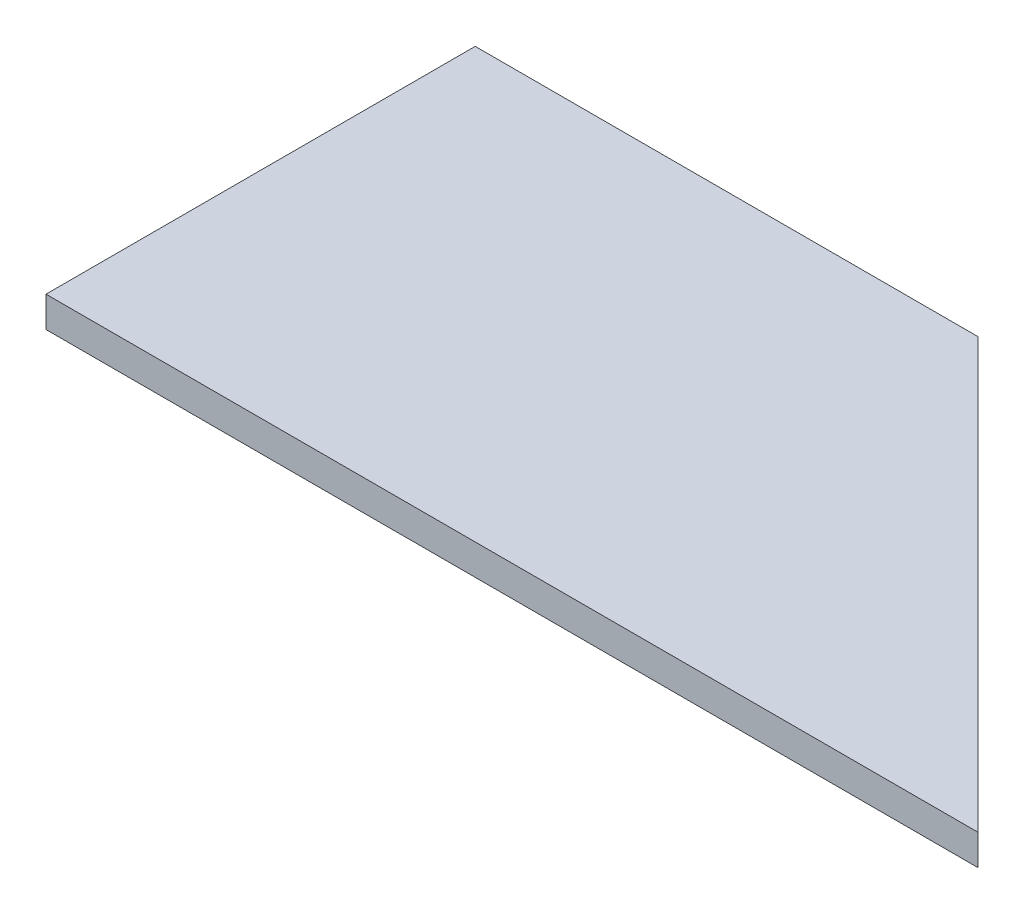
SolidWorks part; units mm, degrees
ref_plane "Front Plane" through (0, 0, 0) normal (0, 0, 1) x (1, 0, 0)
ref_plane "Top Plane" through (0, 0, 0) normal (0, 1, 0) x (1, 0, 0)
ref_plane "Right Plane" through (0, 0, 0) normal (1, 0, 0) x (0, 0, -1)
sketch "Sketch1" plane through (0, 0, 0) normal (0, 1, 0) x (1, 0, 0)
  line L0 (45.6, -21) -> (3.5957, 21)
  line L1 (-45.6, 21) -> (3.5957, 21)
  line L2 (-45.6, 21) -> (-45.6, -21)
  line L3 (-45.6, -21) -> (45.6, -21)
  point P0 (0, 0)
  dimension "D1" = 42
  dimension "D2" = 91.2
  dimension "D3" = 59.4
  dimension "D4" = 49.1957
extrude "Boss-Extrude1" add sketch "Sketch1" along normal blind 3
